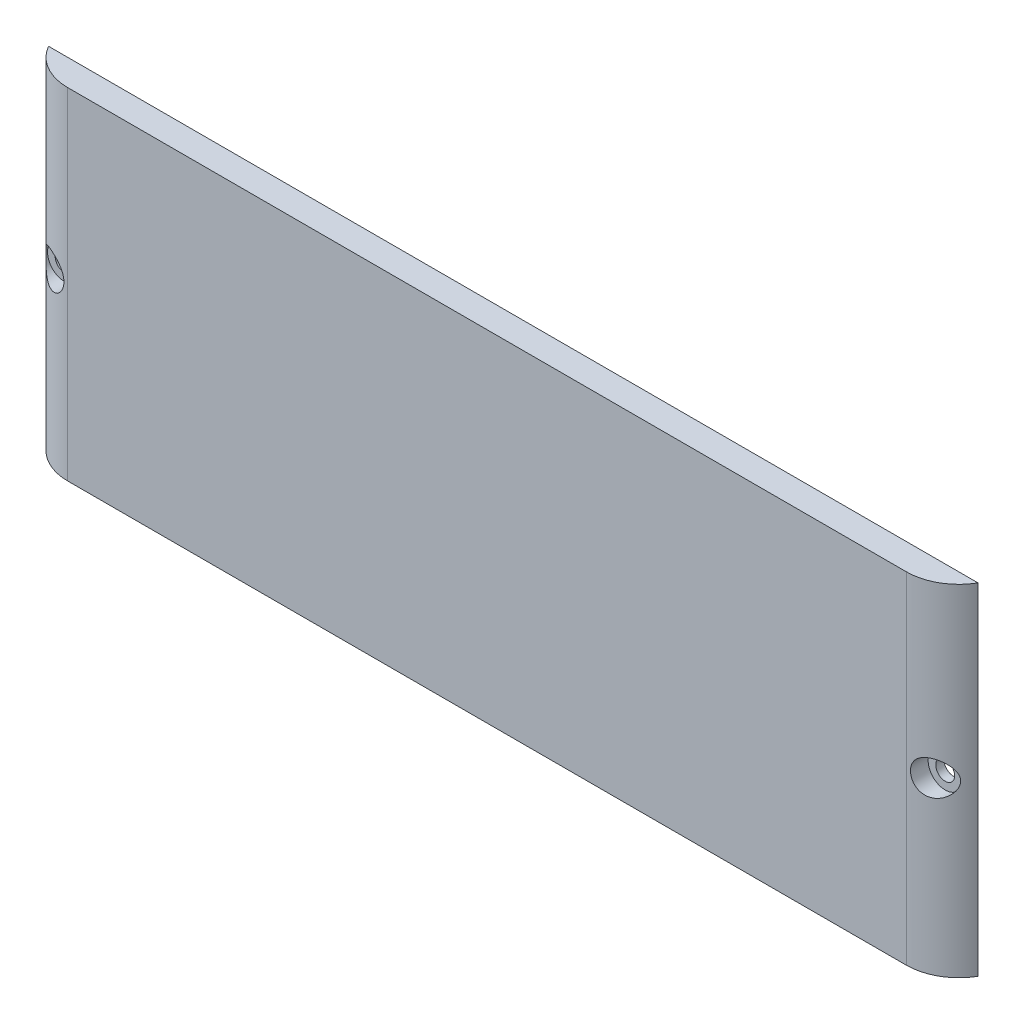
SolidWorks part; units mm, degrees
material "Allzweck-PBT"
ref_plane "Ebene vorne" through (0, 0, 0) normal (0, 0, 1) x (1, 0, 0)
ref_plane "Ebene oben" through (0, 0, 0) normal (0, 1, 0) x (1, 0, 0)
ref_plane "Ebene rechts" through (0, 0, 0) normal (1, 0, 0) x (0, 0, -1)
sketch "Skizze1" plane through (0, 0, 0) normal (0, 0, 1) x (1, 0, 0)
  line L1 (90, 32.5) -> (-90, 32.5)
  line L2 (90, 32.5) -> (90, -32.5)
  line L3 (90, -32.5) -> (-90, -32.5)
  line L4 (-90, 32.5) -> (-90, -32.5)
  line L5 (90, 32.5) -> (-90, -32.5) construction
  line L6 (90, -32.5) -> (-90, 32.5) construction
  point P0 (0, 0)
  dimension "D1" = 180
  dimension "D2" = 65
extrude "Aufsatz-Linear austragen1" add sketch "Skizze1" along normal blind 5
hole_wizard "Stirnsenkung für M3 Zylinderschraube mit Innensechskant1" positions "Skizze4" profile "Skizze5" counterbore size "M3" standard "DIN"
sketch "Skizze4" plane through (0, 0, 5) normal (0, 0, 1) x (1, 0, 0)
  line L0 (-90, 32.5) -> (-90, -32.5) construction
  line L1 (90, -32.5) -> (90, 32.5) construction
  point P0 (-84, 0)
  point P2 (84, 0)
  dimension "D1" = 6
  dimension "6" = 6
sketch "Skizze5" plane through (-84, 0, 5) normal (1, 0, 0) x (0, -1, 0)
  line L0 (0, 0) -> (0, 10.1815)
  line L1 (0, 10.1815) -> (1.8, 9.1)
  line L2 (1.8, 9.1) -> (1.8, 3.4)
  line L3 (1.8, 3.4) -> (3.25, 3.4)
  line L4 (3.25, 3.4) -> (3.25, 0)
  line L5 (3.25, 0) -> (0, 0)
  line L10 (0, 10.1815) -> (-1.8, 9.1) construction
  line L11 (0, -6.35) -> (0, 107.95) construction
  dimension "Bohrerdurchmesser" = 3.6
  dimension "Bohrungstiefe" = 9.1
  dimension "Senkdurchmesser2" = 6.5
  dimension "Senktiefe2" = 3.4
  dimension "Spitzenwinkel" = 118
sketch "Skizze6" plane through (0, 32.5, 0) normal (0, 1, 0) x (1, 0, 0)
  line L0 (-90, -5) -> (-90, 5)
  line L5 (-80, -5) -> (-90, -5)
  line L6 (80, -5) -> (90, -5)
  line L7 (90, -5) -> (90, 5)
  arc A0 (80, -5) -> (90, 5) centre (80, 5) ccw
  arc A1 (-80, -5) -> (-90, 5) centre (-80, 5) cw
  point P9 (-90, -5)
  dimension "D1" = 10
  dimension "D2" = 10
  dimension "D3" = 10
  dimension "D4" = 10
  dimension "D5" = 10
extrude "Schnitt-Linear austragen1" cut sketch "Skizze6" against normal through all
